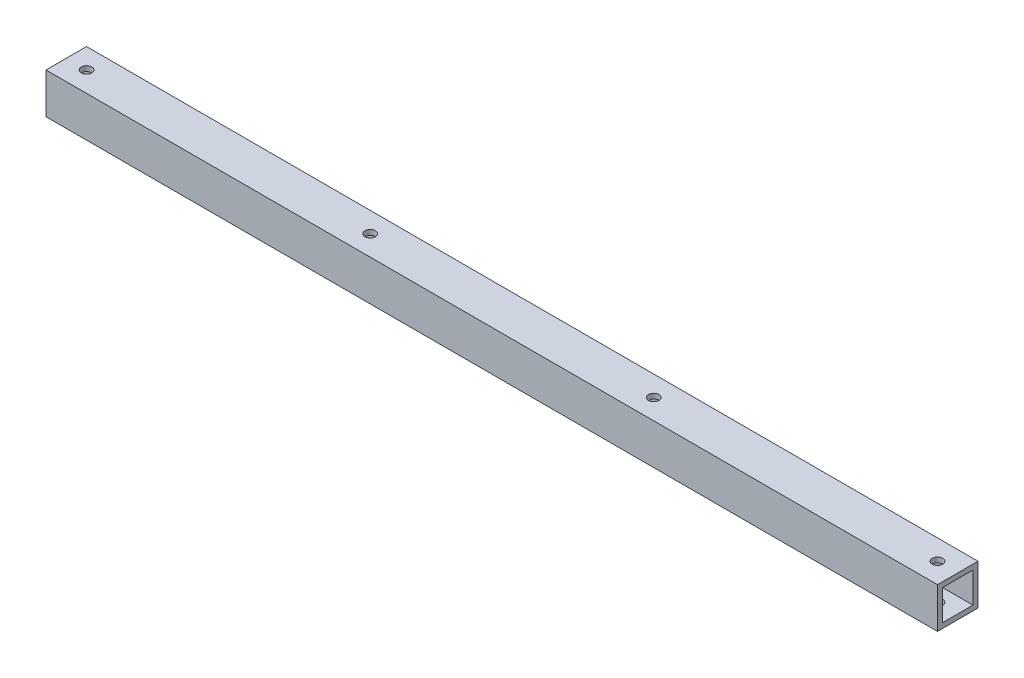
SolidWorks part; units mm, degrees
material "6061 Alloy"
ref_plane "Front Plane" through (0, 0, 0) normal (0, 0, 1) x (1, 0, 0)
ref_plane "Top Plane" through (0, 0, 0) normal (0, 1, 0) x (1, 0, 0)
ref_plane "Right Plane" through (0, 0, 0) normal (1, 0, 0) x (0, 0, -1)
sketch "Sketch1" plane through (0, 0, 0) normal (1, 0, 0) x (0, 0, -1)
  line L0 (3.175, 3.175) -> (22.225, 3.175)
  line L1 (0, 0) -> (25.4, 0)
  line L2 (0, 0) -> (0, 25.4)
  line L3 (0, 25.4) -> (25.4, 25.4)
  line L4 (25.4, 0) -> (25.4, 25.4)
  line L5 (22.225, 3.175) -> (22.225, 22.225)
  line L6 (3.175, 22.225) -> (22.225, 22.225)
  line L7 (3.175, 3.175) -> (3.175, 22.225)
  dimension "D1" = 25.4
  dimension "D2" = 25.4
  dimension "D3" = 3.175
extrude "Extrude1" add sketch "Sketch1" along normal blind 558.8
sketch "Sketch2" plane through (0, 25.4, 0) normal (0, 1, 0) x (-1, 0, 0)
  line L0 (-558.8, -12.7) -> (0, -12.7) construction
  line L1 (-558.8, -25.4) -> (-558.8, 0) construction
  line L2 (0, -25.4) -> (0, 0) construction
  line L3 (-279.4, 0) -> (-279.4, -25.4) construction
  line L4 (-558.8, 0) -> (0, 0) construction
  line L5 (-558.8, -25.4) -> (0, -25.4) construction
  circle A0 centre (-546.1, -12.7) radius 3.2639
  circle A1 centre (-368.3, -12.7) radius 3.2639
  circle A3 centre (-190.5, -12.7) radius 3.2639
  circle A4 centre (-12.7, -12.7) radius 3.2639
  dimension "D1" = 6.5278
  dimension "D2" = 6.5278
  dimension "D3" = 12.7
  dimension "D4" = 177.8
extrude "Cut-Extrude1" cut sketch "Sketch2" against normal through all
